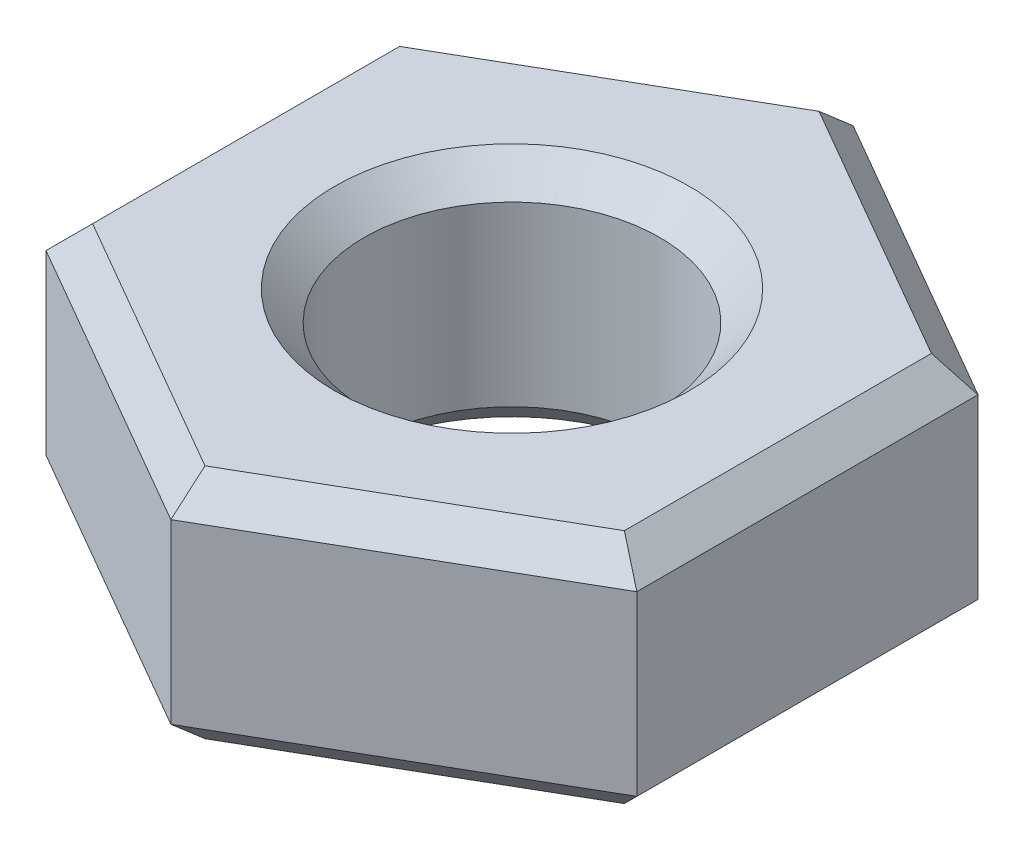
SolidWorks part; units mm, degrees
ref_plane "Front Plane" through (0, 0, 0) normal (0, 0, 1) x (1, 0, 0)
ref_plane "Top Plane" through (0, 0, 0) normal (0, 1, 0) x (1, 0, 0)
ref_plane "Right Plane" through (0, 0, 0) normal (1, 0, 0) x (0, 0, -1)
sketch "Sketch1" plane through (0, 0, 0) normal (0, 1, 0) x (1, 0, 0)
  line L1 (0, -2.8868) -> (2.5, -1.4434)
  line L2 (2.5, -1.4434) -> (2.5, 1.4434)
  line L3 (2.5, 1.4434) -> (0, 2.8868)
  line L4 (0, 2.8868) -> (-2.5, 1.4434)
  line L5 (-2.5, 1.4434) -> (-2.5, -1.4434)
  line L6 (-2.5, -1.4434) -> (0, -2.8868)
  circle A0 centre (0, 0) radius 2.5 construction
  circle A1 centre (0, 0) radius 1.25
  dimension "D2" = 2.5
  dimension "D1" = 5
extrude "Boss-Extrude1" add sketch "Sketch1" along normal blind 2
chamfer "Chamfer1" distance 0.25 angle 45 14 edges at (0, 0, 1.25) (1.25, 0, 2.1651) (2.5, 0, 0) (1.25, 0, -2.1651) (-1.25, 0, -2.1651) (-2.5, 0, 0) (-1.25, 0, 2.1651) (0, 2, 1.25) (-2.5, 2, 0) (-1.25, 2, -2.1651) (1.25, 2, -2.1651) (2.5, 2, 0) (1.25, 2, 2.1651) (-1.25, 2, 2.1651)
